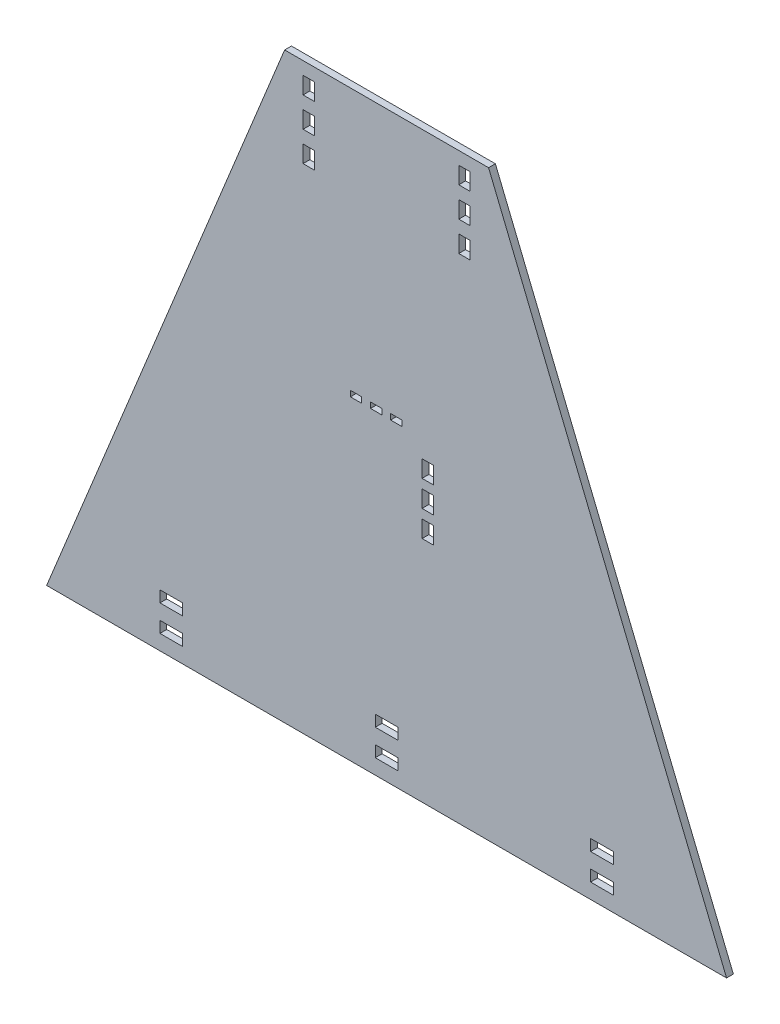
SolidWorks part; units mm, degrees
ref_plane "Front Plane" through (0, 0, 0) normal (0, 0, 1) x (1, 0, 0)
ref_plane "Top Plane" through (0, 0, 0) normal (0, 1, 0) x (1, 0, 0)
ref_plane "Right Plane" through (0, 0, 0) normal (1, 0, 0) x (0, 0, -1)
sketch "Sketch1" plane through (0, 0, 0) normal (0, 0, 1) x (1, 0, 0)
  line L0 (0, 0) -> (300.025, 734.6932) construction
  line L1 (300.025, 734.6932) -> (600.05, 0) construction
  line L2 (296.475, 0) -> (0, 0)
  line L3 (300.025, 734.6932) -> (300.025, 498.6) construction
  line L4 (300.025, 498.6) -> (300.025, 262.5068) construction
  line L5 (300.025, 262.5068) -> (300.025, 0) construction
  line L6 (390.025, 514.3036) -> (600.05, 0)
  line L7 (210.025, 514.3036) -> (0, 0)
  line L8 (490.05, 13.3333) -> (490.05, 0) construction
  line L9 (490.05, 36.6667) -> (490.05, 23.3333) construction
  line L10 (105.0125, 257.1518) -> (495.0375, 257.1518) construction
  line L11 (296.475, 0) -> (300.025, 0)
  line L12 (73.8825, 60) -> (185.8654, 60) construction
  line L13 (300.025, 0) -> (600.05, 0)
  line L14 (100, 13.3333) -> (120, 13.3333)
  line L15 (100, 13.3333) -> (100, 23.3333)
  line L16 (100, 23.3333) -> (120, 23.3333)
  line L17 (120, 13.3333) -> (120, 23.3333)
  line L18 (100, 36.6667) -> (120, 36.6667)
  line L19 (100, 36.6667) -> (100, 46.6667)
  line L20 (100, 46.6667) -> (120, 46.6667)
  line L21 (120, 36.6667) -> (120, 46.6667)
  line L22 (110, 46.6667) -> (110, 60) construction
  line L23 (110, 36.6667) -> (110, 23.3333) construction
  line L24 (110, 13.3333) -> (110, 0) construction
  line L25 (490.05, 46.6667) -> (490.05, 60) construction
  line L26 (480.05, 36.6667) -> (480.05, 46.6667)
  line L27 (500.05, 46.6667) -> (480.05, 46.6667)
  line L28 (500.05, 36.6667) -> (500.05, 46.6667)
  line L29 (500.05, 36.6667) -> (480.05, 36.6667)
  line L30 (480.05, 13.3333) -> (480.05, 23.3333)
  line L31 (500.05, 23.3333) -> (480.05, 23.3333)
  line L32 (500.05, 13.3333) -> (500.05, 23.3333)
  line L33 (500.05, 13.3333) -> (480.05, 13.3333)
  line L34 (313.575, 283.1998) -> (313.575, 278.1998) construction
  line L35 (303.575, 280.6998) -> (295.825, 280.6998) construction
  line L36 (313.575, 283.1998) -> (303.575, 283.1998)
  line L37 (313.575, 283.1998) -> (313.575, 278.1998)
  line L38 (313.575, 278.1998) -> (303.575, 278.1998)
  line L39 (303.575, 283.1998) -> (303.575, 278.1998)
  line L40 (295.825, 283.1998) -> (285.825, 283.1998)
  line L41 (295.825, 283.1998) -> (295.825, 278.1998)
  line L42 (295.825, 278.1998) -> (285.825, 278.1998)
  line L43 (285.825, 283.1998) -> (285.825, 278.1998)
  line L44 (278.075, 283.1998) -> (268.075, 283.1998)
  line L45 (278.075, 283.1998) -> (278.075, 278.1998)
  line L46 (278.075, 278.1998) -> (268.075, 278.1998)
  line L47 (268.075, 283.1998) -> (268.075, 278.1998)
  line L48 (285.825, 280.6998) -> (278.075, 280.6998) construction
  line L50 (368.725, 503.0536) -> (368.725, 514.3036) construction
  line L51 (363.725, 503.0536) -> (373.725, 503.0536)
  line L52 (363.725, 503.0536) -> (363.725, 488.0536)
  line L53 (363.725, 488.0536) -> (373.725, 488.0536)
  line L54 (373.725, 503.0536) -> (373.725, 488.0536)
  line L55 (300.025, 426.9288) -> (300.025, 498.6) construction
  line L56 (113.6078, 278.1998) -> (486.4422, 278.1998) construction
  line L57 (296.475, 525.0136) -> (296.475, 0) construction
  line L58 (115.6497, 283.1998) -> (484.4003, 283.1998) construction
  line L59 (300.025, 262.5068) -> (300.025, 278.1998) construction
  line L60 (300.025, 278.1998) -> (300.025, 283.1998) construction
  line L61 (300.025, 283.1998) -> (296.475, 283.1998) construction
  line L62 (296.475, 283.1998) -> (296.475, 278.1998) construction
  line L63 (296.475, 278.1998) -> (296.475, 262.5068) construction
  line L64 (296.475, 262.5068) -> (300.025, 262.5068) construction
  line L65 (331.325, 439.8577) -> (331.325, 0) construction
  line L78 (341.325, 439.8577) -> (341.325, 0) construction
  line L79 (107.1993, 262.5068) -> (492.8507, 262.5068) construction
  line L80 (331.325, 262.5068) -> (341.325, 262.5068) construction
  line L81 (341.325, 262.5068) -> (341.325, 219.9288) construction
  line L83 (331.325, 219.9288) -> (331.325, 262.5068) construction
  line L84 (363.725, 476.8036) -> (373.725, 476.8036)
  line L85 (331.325, 262.5068) -> (341.325, 262.5068)
  line L86 (331.325, 262.5068) -> (331.325, 247.5068)
  line L87 (331.325, 247.5068) -> (341.325, 247.5068)
  line L88 (341.325, 262.5068) -> (341.325, 247.5068)
  line L89 (331.325, 239.5068) -> (341.325, 239.5068)
  line L90 (331.325, 239.5068) -> (331.325, 224.5068)
  line L91 (331.325, 224.5068) -> (341.325, 224.5068)
  line L92 (341.325, 239.5068) -> (341.325, 224.5068)
  line L93 (331.325, 216.5068) -> (341.325, 216.5068)
  line L94 (331.325, 216.5068) -> (331.325, 201.5068)
  line L95 (331.325, 201.5068) -> (341.325, 201.5068)
  line L96 (341.325, 216.5068) -> (341.325, 201.5068)
  line L97 (363.725, 476.8036) -> (363.725, 461.8036)
  line L98 (363.725, 461.8036) -> (373.725, 461.8036)
  line L99 (373.725, 476.8036) -> (373.725, 461.8036)
  line L100 (363.725, 450.5536) -> (373.725, 450.5536)
  line L101 (363.725, 450.5536) -> (363.725, 435.5536)
  line L102 (363.725, 435.5536) -> (373.725, 435.5536)
  line L103 (373.725, 450.5536) -> (373.725, 435.5536)
  line L104 (368.725, 488.0536) -> (368.725, 476.8036) construction
  line L105 (368.725, 461.8036) -> (368.725, 450.5536) construction
  line L107 (368.725, 435.5536) -> (368.725, 424.3036) construction
  line L108 (231.325, 435.5536) -> (231.325, 424.3036) construction
  line L109 (231.325, 461.8036) -> (231.325, 450.5536) construction
  line L110 (231.325, 488.0536) -> (231.325, 476.8036) construction
  line L111 (231.325, 503.0536) -> (231.325, 514.3036) construction
  line L112 (226.325, 450.5536) -> (226.325, 435.5536)
  line L113 (236.325, 435.5536) -> (226.325, 435.5536)
  line L114 (236.325, 450.5536) -> (236.325, 435.5536)
  line L115 (236.325, 450.5536) -> (226.325, 450.5536)
  line L116 (226.325, 476.8036) -> (226.325, 461.8036)
  line L117 (236.325, 461.8036) -> (226.325, 461.8036)
  line L118 (236.325, 476.8036) -> (236.325, 461.8036)
  line L119 (236.325, 476.8036) -> (226.325, 476.8036)
  line L120 (226.325, 503.0536) -> (226.325, 488.0536)
  line L121 (236.325, 488.0536) -> (226.325, 488.0536)
  line L122 (236.325, 503.0536) -> (236.325, 488.0536)
  line L123 (236.325, 503.0536) -> (226.325, 503.0536)
  line L125 (210.025, 514.3036) -> (390.025, 514.3036)
  line B0 (300.025, 13.3333) -> (300.025, 0) construction
  line B1 (300.025, 36.6667) -> (300.025, 23.3333) construction
  line B2 (300.025, 46.6667) -> (300.025, 60) construction
  line B3 (290.025, 36.6667) -> (290.025, 46.6667)
  line B4 (310.025, 46.6667) -> (290.025, 46.6667)
  line B5 (310.025, 36.6667) -> (310.025, 46.6667)
  line B6 (310.025, 36.6667) -> (290.025, 36.6667)
  line B7 (290.025, 13.3333) -> (290.025, 23.3333)
  line B8 (310.025, 23.3333) -> (290.025, 23.3333)
  line B9 (310.025, 13.3333) -> (310.025, 23.3333)
  line B10 (310.025, 13.3333) -> (290.025, 13.3333)
  dimension "D23" = 15
  dimension "D1" = 600.05
  dimension "D3" = 60
  dimension "D4" = 20
  dimension "D5" = 10
  dimension "D6" = 100
  dimension "D7" = 192.8257
  dimension "D8" = 127.4
  dimension "D9" = 90
  dimension "D10" = 10
  dimension "D11" = 21.048
  dimension "D12" = 3.55
  dimension "D13" = 5
  dimension "D14" = 10
  dimension "D15" = 17.75
  dimension "D16" = 7.75
  dimension "D17" = 31.3
  dimension "D18" = 10
  dimension "D19" = 5.355
  dimension "D20" = 15
  dimension "D21" = 8
  dimension "D22" = 8
  dimension "D24" = 180
  dimension "D25" = 192.8257
  dimension "D26" = 514.3036
sketch_block_instance "Block3-1"
sketch_block "Block3"
extrude "Boss-Extrude1" add sketch "Sketch1" along normal blind 6
